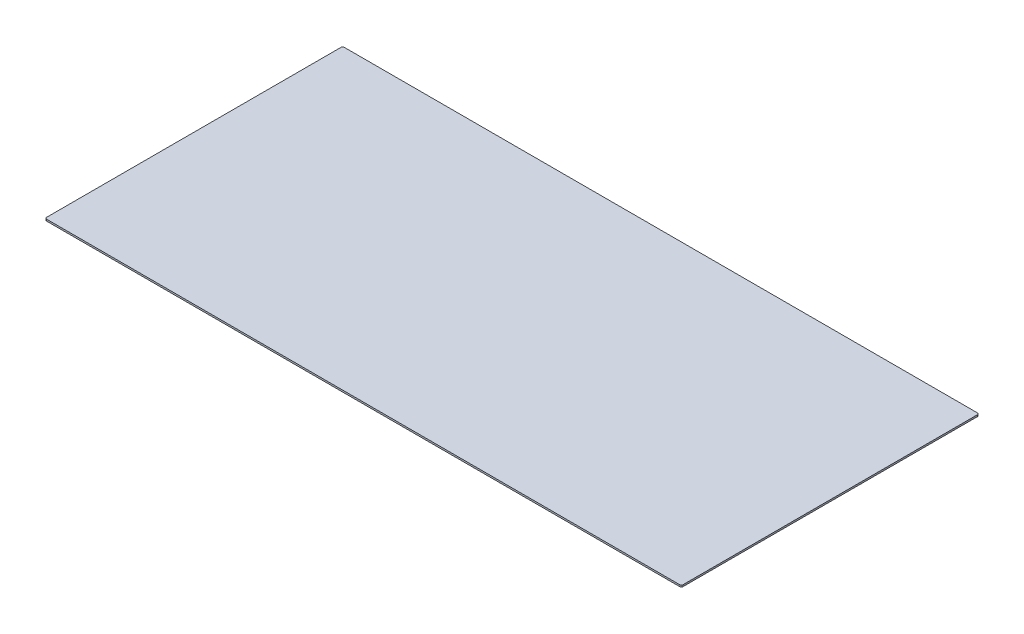
SolidWorks part; units mm, degrees
material "PE High Density"
ref_plane "Front Plane" through (0, 0, 0) normal (0, 0, 1) x (1, 0, 0)
ref_plane "Top Plane" through (0, 0, 0) normal (0, 1, 0) x (1, 0, 0)
ref_plane "Right Plane" through (0, 0, 0) normal (1, 0, 0) x (0, 0, -1)
sketch "Sketch1" plane through (0, 0, 0) normal (0, 1, 0) x (1, 0, 0)
  line L1 (-587.375, -276.225) -> (587.375, -276.225)
  line L2 (-590.55, -273.05) -> (-590.55, 273.05)
  line L3 (-587.375, 276.225) -> (587.375, 276.225)
  line L4 (590.55, -273.05) -> (590.55, 273.05)
  line L5 (-590.55, -276.225) -> (590.55, 276.225) construction
  line L6 (-590.55, 276.225) -> (590.55, -276.225) construction
  arc A0 (587.375, 276.225) -> (590.55, 273.05) centre (587.375, 273.05) cw
  arc A1 (587.375, -276.225) -> (590.55, -273.05) centre (587.375, -273.05) ccw
  arc A2 (-587.375, -276.225) -> (-590.55, -273.05) centre (-587.375, -273.05) cw
  arc A3 (-590.55, 273.05) -> (-587.375, 276.225) centre (-587.375, 273.05) cw
  point P0 (0, 0)
  dimension "D3" = 3.175
  dimension "D1" = 1181.1
  dimension "D2" = 552.45
extrude "Boss-Extrude1" add sketch "Sketch1" along normal blind 3.175
sketch "Sketch2" plane through (0, 3.175, 0) normal (0, 1, 0) x (1, 0, 0)
  line L0 (587.375, 276.225) -> (-587.375, 276.225) construction
  line L1 (-590.55, 273.05) -> (-590.55, -273.05) construction
  line L2 (587.375, 276.225) -> (-587.375, 276.225) construction
  line L3 (590.55, -273.05) -> (590.55, 273.05) construction
  line L4 (-587.375, -276.225) -> (587.375, -276.225) construction
  point P0 (-406.4, 219.075)
  point P5 (0, 219.075)
  point P7 (406.4, 219.075)
  point P20 (-406.4, 238.125)
  point P21 (406.4, -266.573)
  point P29 (0, -266.573)
  point P31 (-406.4, -266.573)
  point P35 (0, 238.125)
  point P51 (406.4, 238.125)
  dimension "D1" = 57.15
  dimension "D2" = 9.652
  dimension "D3" = 184.15
  dimension "D4" = 406.4
  dimension "D5" = 406.4
  dimension "D6" = 406.4
  dimension "D7" = 184.15
  dimension "D9" = 406.4
  dimension "D10" = 9.652
  dimension "D13" = 38.1
  dimension "D14" = 184.15
hole_wizard "1/4 (0.25) Diameter Hole1" [suppressed] positions "Sketch3" profile "Sketch4" hole size "1/4" standard "ANSI Inch"
sketch "Sketch3" plane through (0, 3.175, 0) normal (0, 1, 0) x (1, 0, 0)
  point P0 (-406.4, 219.075)
  point P6 (0, 219.075)
  point P12 (406.4, 219.075)
  point P54 (-406.4, -266.573)
  point P60 (0, -266.573)
  point P66 (406.4, -266.573)
  point P69 (-406.4, 238.125)
  point P75 (0, 238.125)
  point P81 (406.4, 238.125)
sketch "Sketch4" plane through (-406.4, 3.175, -219.075) normal (1, 0, 0) x (0, 0, 1)
  line L0 (0, 0) -> (0, 3.175)
  line L1 (0, 3.175) -> (3.175, 3.175)
  line L2 (3.175, 3.175) -> (3.175, 0)
  line L5 (3.175, 0) -> (0, 0)
  line L11 (0, -6.35) -> (0, 107.95) construction
  dimension "Thru Hole Dia." = 6.35
  dimension "Thru Hole Depth" = 3.175
sketch "Sketch5" [suppressed] plane through (0, 3.175, 0) normal (0, 1, 0) x (1, 0, 0)
  line L0 (-590.55, 273.05) -> (-590.55, -273.05) construction
  line L3 (590.55, -273.05) -> (590.55, 273.05) construction
  line L33 (587.375, 276.225) -> (-587.375, 276.225) construction
  line L36 (-419.1, 193.675) -> (-393.7, 193.675) construction
  line L37 (-419.1, 206.375) -> (-393.7, 206.375)
  line L38 (-419.1, 180.975) -> (-393.7, 180.975)
  line L42 (-12.7, 193.675) -> (12.7, 193.675) construction
  line L43 (-12.7, 206.375) -> (12.7, 206.375)
  line L44 (-12.7, 180.975) -> (12.7, 180.975)
  line L48 (393.7, 193.675) -> (419.1, 193.675) construction
  line L49 (393.7, 206.375) -> (419.1, 206.375)
  line L50 (393.7, 180.975) -> (419.1, 180.975)
  line L51 (-403.225, 219.075) -> (-406.4, 219.075) construction
  circle A2 centre (0, 219.075) radius 3.175 construction
  arc A22 (-419.1, 206.375) -> (-419.1, 180.975) centre (-419.1, 193.675) ccw
  arc A23 (-393.7, 180.975) -> (-393.7, 206.375) centre (-393.7, 193.675) ccw
  arc A26 (-12.7, 206.375) -> (-12.7, 180.975) centre (-12.7, 193.675) ccw
  arc A27 (12.7, 180.975) -> (12.7, 206.375) centre (12.7, 193.675) ccw
  arc A30 (393.7, 206.375) -> (393.7, 180.975) centre (393.7, 193.675) ccw
  arc A31 (419.1, 180.975) -> (419.1, 206.375) centre (419.1, 193.675) ccw
  circle A32 centre (-406.4, 219.075) radius 3.175 construction
  circle A33 centre (406.4, 219.075) radius 3.175 construction
  point P95 (-406.4, 193.675)
  point P109 (0, 193.675)
  point P123 (406.4, 193.675)
  dimension "D2" = 184.15
  dimension "D3" = 406.4
  dimension "D4" = 406.4
  dimension "D5" = 184.15
  dimension "D6" = 12.7
  dimension "D7" = 12.7
  dimension "D10" = 12.7
  dimension "D11" = 25.4
  dimension "D12" = 25.4
extrude "Cut-Extrude1" [suppressed] cut sketch "Sketch5" against normal through all
